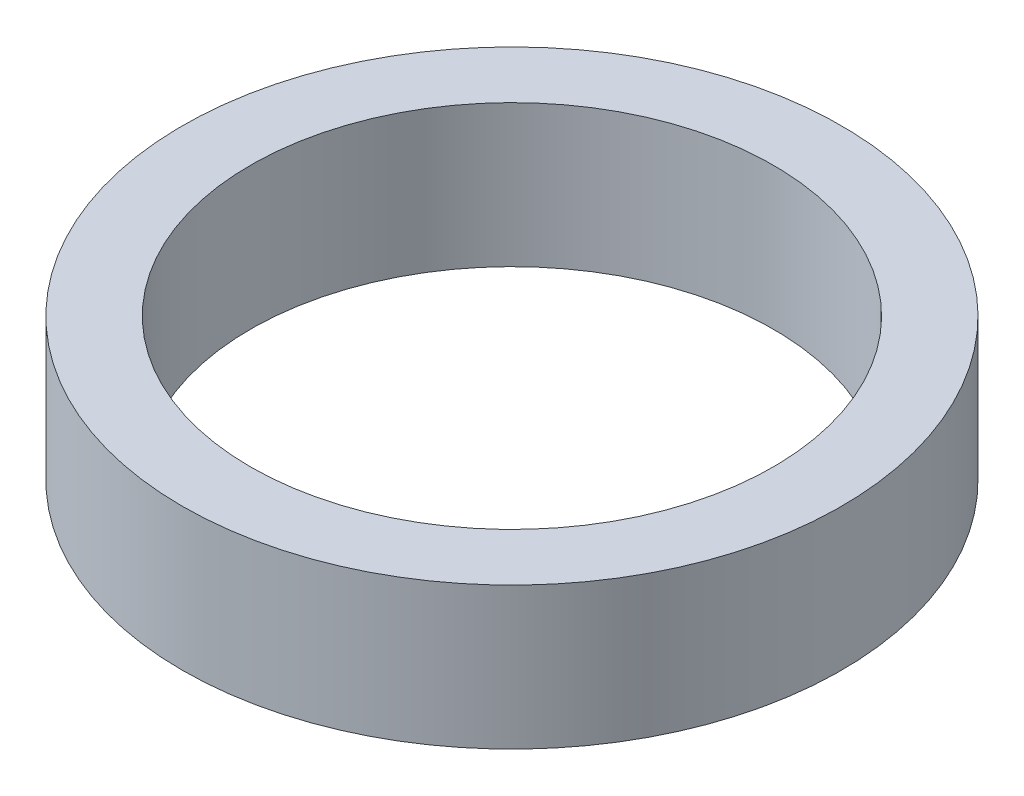
SolidWorks part; units mm, degrees
material "Rubber"
ref_plane "Front Plane" through (0, 0, 0) normal (0, 0, 1) x (1, 0, 0)
ref_plane "Top Plane" through (0, 0, 0) normal (0, 1, 0) x (1, 0, 0)
ref_plane "Right Plane" through (0, 0, 0) normal (1, 0, 0) x (0, 0, -1)
sketch "Sketch1" plane through (0, 0, 0) normal (0, 1, 0) x (1, 0, 0)
  circle A0 centre (0, 0) radius 290
  dimension "D1" = 580
extrude "Boss-Extrude1" add sketch "Sketch1" along normal blind 125
sketch "Sketch2" plane through (0, 125, 0) normal (0, 1, 0) x (1, 0, 0)
  circle A0 centre (0, 0) radius 230
  dimension "D1" = 460
extrude "Cut-Extrude1" cut sketch "Sketch2" against normal through all
